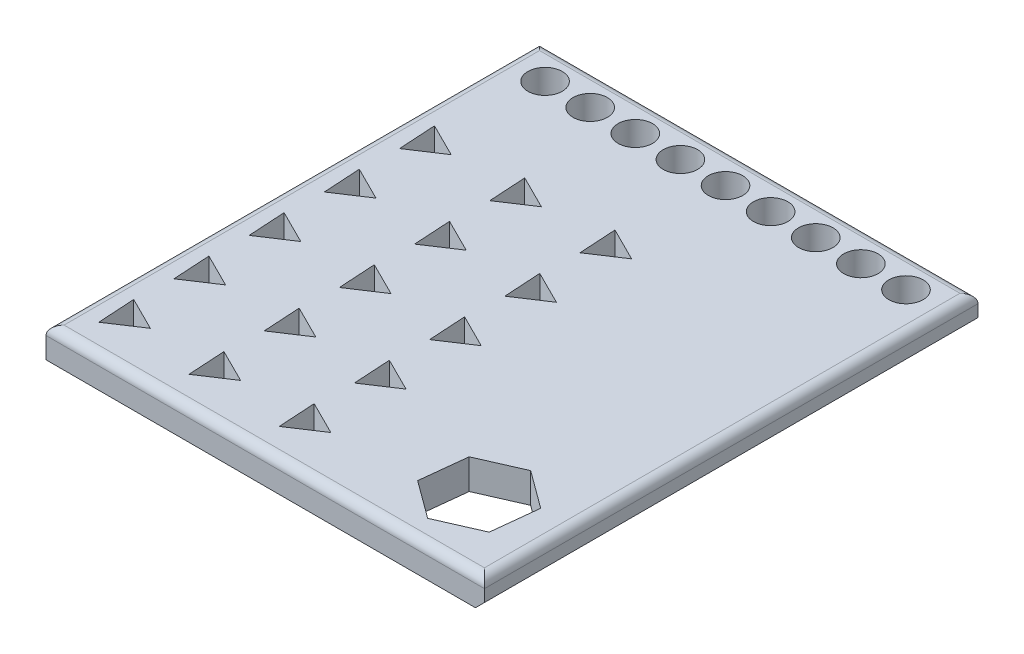
SolidWorks part; units mm, degrees
ref_plane "Front Plane" through (0, 0, 0) normal (0, 0, 1) x (1, 0, 0)
ref_plane "Top Plane" through (0, 0, 0) normal (0, 1, 0) x (1, 0, 0)
ref_plane "Right Plane" through (0, 0, 0) normal (1, 0, 0) x (0, 0, -1)
sketch "Sketch1" plane through (0, 0, 0) normal (0, 1, 0) x (1, 0, 0)
  line L1 (-72.8873, 82.0423) -> (72.8873, 82.0423)
  line L2 (-72.8873, 82.0423) -> (-72.8873, -82.0423)
  line L3 (-72.8873, -82.0423) -> (72.8873, -82.0423)
  line L4 (72.8873, 82.0423) -> (72.8873, -82.0423)
  line L5 (41.6379, -46.8678) -> (41.6594, -46.892) construction
  line L7 (60.3993, -67.9857) -> (62.0959, -52.5586)
  line L8 (62.0959, -52.5586) -> (49.5839, -43.3757)
  line L9 (49.5839, -43.3757) -> (35.3754, -49.62)
  line L10 (35.3754, -49.62) -> (33.6788, -65.0471)
  line L11 (33.6788, -65.0471) -> (46.1907, -74.2299)
  line L12 (46.1907, -74.2299) -> (60.3993, -67.9857)
  circle A0 centre (47.8873, -58.8028) radius 13.4408 construction
  point P0 (0, 0)
  dimension "D1" = 25
extrude "Boss-Extrude1" add sketch "Sketch1" along normal blind 10
fillet "Fillet1" radius 3 4 edges at (0, 10, -82.0423) (-72.8873, 10, 0) (72.8873, 10, 0) (0, 10, 82.0423)
sketch "Sketch2" plane through (0, 10, 0) normal (0, 1, 0) x (1, 0, 0)
  circle A0 centre (-60.0913, 71.0836) radius 5.7183
extrude "Cut-Extrude1" cut sketch "Sketch2" against normal blind 10
pattern_linear "LPattern1" count 9 spacing 15 along (1, 0, 0) of "Cut-Extrude1"
sketch "Sketch3" plane through (0, 10, 0) normal (0, 1, 0) x (1, 0, 0)
  line L1 (-64.9402, 27.5504) -> (-54.6047, 34.3745)
  line L2 (-54.6047, 34.3745) -> (-65.6823, 39.9132)
  line L3 (-65.6823, 39.9132) -> (-64.9402, 27.5504)
  circle A0 centre (-61.7424, 33.946) radius 3.5753 construction
extrude "Cut-Extrude2" cut sketch "Sketch3" against normal blind 10
pattern_linear "LPattern2" count 5 spacing 25 along (0, 0, 1) count 3 spacing 30 along (1, 0, 0) of "Cut-Extrude2"
chamfer "Chamfer1" distance 3 angle 45 2 edges at (72.8873, 0, 0) (0, 0, -82.0423)
